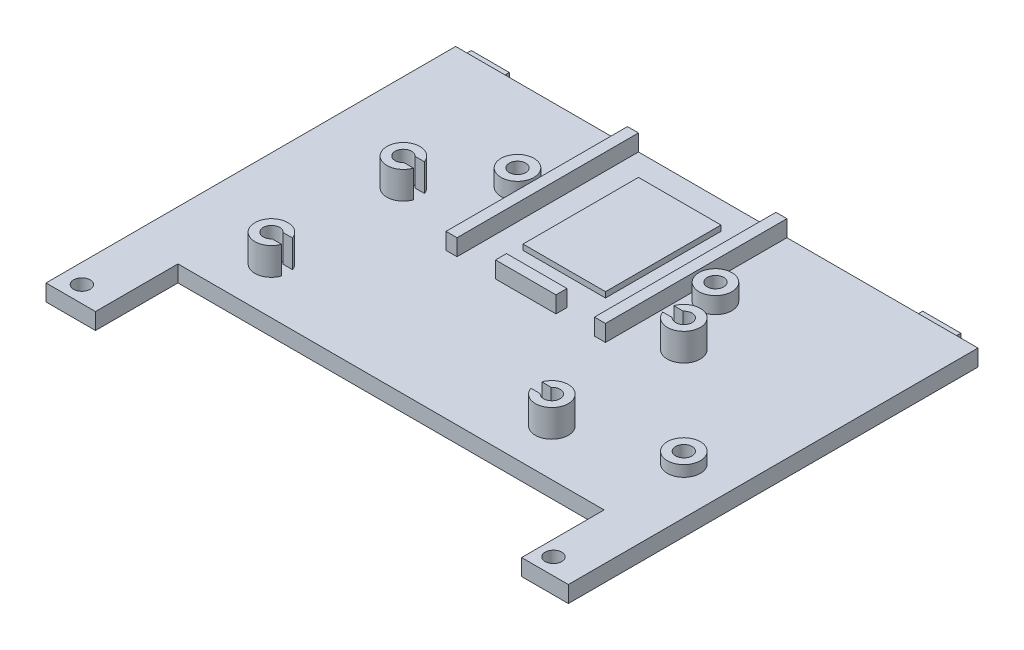
SolidWorks part; units mm, degrees
ref_plane "Front Plane" through (0, 0, 0) normal (0, 0, 1) x (1, 0, 0)
ref_plane "Top Plane" through (0, 0, 0) normal (0, 1, 0) x (1, 0, 0)
ref_plane "Right Plane" through (0, 0, 0) normal (1, 0, 0) x (0, 0, -1)
sketch "Sketch1" plane through (0, 0, 0) normal (0, 1, 0) x (1, 0, 0)
  line L1 (-53.25, 37.25) -> (53.25, 37.25)
  line L2 (-53.25, 37.25) -> (-53.25, -37.25)
  line L3 (-53.25, -37.25) -> (53.25, -37.25)
  line L4 (53.25, 37.25) -> (53.25, -37.25)
  dimension "D1" = 106.5
  dimension "D2" = 74.5
  dimension "D3" = 37.25
  dimension "D4" = 53.25
extrude "Boss-Extrude1" add sketch "Sketch1" along normal blind 3
sketch "Sketch2" plane through (0, 3, 0) normal (0, 1, 0) x (1, 0, 0)
  line L0 (53.25, 37.25) -> (-53.25, 37.25) construction
  line L1 (-47.265, 37.25) -> (-40.335, 37.25)
  line L2 (-47.265, 37.25) -> (-47.265, 39.1)
  line L3 (-47.265, 39.1) -> (-40.335, 39.1)
  line L4 (-40.335, 37.25) -> (-40.335, 39.1)
  line L5 (-53.25, 37.25) -> (-53.25, -37.25) construction
  line L6 (34.85, 37.25) -> (41.78, 37.25)
  line L7 (34.85, 37.25) -> (34.85, 39.1)
  line L8 (34.85, 39.1) -> (41.78, 39.1)
  line L9 (41.78, 37.25) -> (41.78, 39.1)
  line L10 (53.25, -37.25) -> (53.25, 37.25) construction
  dimension "D1" = 5.985
  dimension "D2" = 6.93
  dimension "D3" = 11.47
  dimension "D4" = 1.85
  dimension "D5" = 6.93
  dimension "D6" = 1.85
extrude "Boss-Extrude2" add sketch "Sketch2" against normal blind 3
sketch "Sketch3" plane through (0, 3, 0) normal (0, 1, 0) x (1, 0, 0)
  line L1 (-47.265, 39.1) -> (-40.335, 39.1)
  line L2 (-47.265, 39.1) -> (-47.265, 37.25)
  line L3 (-47.265, 37.25) -> (-40.335, 37.25)
  line L4 (-40.335, 39.1) -> (-40.335, 37.25)
  line L5 (34.85, 39.1) -> (41.78, 39.1)
  line L6 (34.85, 39.1) -> (34.85, 37.25)
  line L7 (34.85, 37.25) -> (41.78, 37.25)
  line L8 (41.78, 39.1) -> (41.78, 37.25)
extrude "Cut-Extrude1" cut sketch "Sketch3" against normal blind 1.07
sketch "Sketch4" plane through (0, 3, 0) normal (0, 1, 0) x (1, 0, 0)
  line L0 (-53.25, 37.25) -> (-53.25, -37.25) construction
  line L1 (-53.25, 32.25) -> (-48.25, 32.25)
  line L2 (-53.25, 32.25) -> (-53.25, -32.25)
  line L3 (-53.25, -32.25) -> (-48.25, -32.25)
  line L4 (-48.25, 32.25) -> (-48.25, -32.25)
  line L5 (53.25, 37.25) -> (-53.25, 37.25) construction
  line L6 (-53.25, -37.25) -> (53.25, -37.25) construction
  line L7 (53.25, -37.25) -> (53.25, 37.25) construction
  line L8 (-39.25, -37.25) -> (39.25, -37.25)
  line L9 (-39.25, -37.25) -> (-39.25, -22.25)
  line L10 (-39.25, -22.25) -> (39.25, -22.25)
  line L11 (39.25, -37.25) -> (39.25, -22.25)
  dimension "D1" = 5
  dimension "D2" = 5
  dimension "D3" = 5
  dimension "D4" = 14
  dimension "D5" = 14
  dimension "D6" = 15
extrude "Cut-Extrude2" cut sketch "Sketch4" against normal blind 3
sketch "Sketch5" plane through (0, 3, 0) normal (0, 1, 0) x (1, 0, 0)
  circle A0 centre (-53.25, -37.25) radius 3.5
  circle A1 centre (53.25, -37.25) radius 3.5
  circle A2 centre (53.25, 37.25) radius 3.5
  circle A3 centre (-53.25, 37.25) radius 3.5
  dimension "D1" = 7
  dimension "D2" = 7
  dimension "D3" = 7
  dimension "D4" = 7
extrude "Cut-Extrude3" cut sketch "Sketch5" against normal blind 3
sketch "Sketch6" plane through (0, 3, 0) normal (0, 1, 0) x (1, 0, 0)
  line L0 (39.25, -22.25) -> (-39.25, -22.25) construction
  line L1 (-33.25, 12.75) -> (22.75, 12.75)
  line L2 (-33.25, 12.75) -> (-33.25, -16.25)
  line L3 (-33.25, -16.25) -> (22.75, -16.25)
  line L4 (22.75, 12.75) -> (22.75, -16.25)
  line L5 (-48.25, -32.25) -> (-48.25, 32.25) construction
  line L7 (-30.75, -14.75) -> (-27.3508, -14.75)
  line L8 (-30.75, -14.75) -> (-30.75, -12.75)
  line L9 (-30.75, -12.75) -> (-27.3508, -12.75)
  line L10 (-27.3508, -14.75) -> (-27.3508, -12.75)
  line L11 (-30.75, 11.25) -> (-27.35, 11.25)
  line L12 (-30.75, 11.25) -> (-30.75, 9.25)
  line L13 (-30.75, 9.25) -> (-27.35, 9.25)
  line L14 (-27.35, 11.25) -> (-27.35, 9.25)
  line L15 (20.25, 9.25) -> (16.85, 9.25)
  line L16 (20.25, 9.25) -> (20.25, 11.25)
  line L17 (20.25, 11.25) -> (16.85, 11.25)
  line L18 (16.85, 9.25) -> (16.85, 11.25)
  line L19 (20.25, -12.75) -> (16.85, -12.75)
  line L20 (20.25, -12.75) -> (20.25, -14.75)
  line L21 (20.25, -14.75) -> (16.85, -14.75)
  line L22 (16.85, -12.75) -> (16.85, -14.75)
  circle A0 centre (-30.75, -13.75) radius 1.5
  circle A1 centre (20.25, -13.75) radius 1.5
  circle A2 centre (20.25, 10.25) radius 1.5
  circle A3 centre (-30.75, 10.25) radius 1.5
  circle A4 centre (-30.75, -13.75) radius 3
  circle A5 centre (20.25, -13.75) radius 3
  circle A6 centre (20.25, 10.25) radius 3
  circle A7 centre (-30.75, 10.25) radius 3
  dimension "D6" = 3
  dimension "D14" = 3
  dimension "D15" = 3
  dimension "D16" = 3
  dimension "D17" = 6
  dimension "D18" = 6
  dimension "D19" = 6
  dimension "D20" = 6
  dimension "D21" = 1
  dimension "D1" = 29
  dimension "D2" = 56
  dimension "D3" = 6
  dimension "D4" = 15
  dimension "D5" = 2.5
  dimension "D7" = 2.5
  dimension "D8" = 2.5
  dimension "D9" = 2.5
  dimension "D10" = 2.5
  dimension "D11" = 2.5
  dimension "D12" = 2.5
  dimension "D13" = 2.5
  dimension "D22" = 2
  dimension "D23" = 3.3992
  dimension "D24" = 0
  dimension "D25" = 0
  dimension "D26" = 1
  dimension "D27" = 2
  dimension "D28" = 3.4
  dimension "D29" = 0
  dimension "D30" = 1
  dimension "D31" = 2
  dimension "D32" = 3.4
  dimension "D33" = 0
  dimension "D34" = 1
  dimension "D35" = 2
  dimension "D36" = 3.4
extrude "Boss-Extrude5" add sketch "Sketch6" along normal blind 5 contours L11 A7 L1 L2 L13 A3 | L2 A7 | L1 A7 | L3 A4 L7 A0 L9 L2 | L2 A4 | L3 A4 | L3 A5 L4 L19 A1 L21 | L3 A5 | L4 A5 | L4 A6 L1 L17 A2 L15 | L4 A6 | L1 A6
sketch "Sketch9" plane through (0, 3, 0) normal (0, 1, 0) x (1, 0, 0)
  line L0 (49.75, 37.25) -> (-49.75, 37.25) construction
  line L1 (53.25, -33.75) -> (53.25, 33.75) construction
  circle A0 centre (38.25, -7.75) radius 3
  circle A1 centre (38.25, -7.75) radius 1.5
  dimension "D3" = 6
  dimension "D4" = 3
  dimension "D1" = 45
  dimension "D2" = 15
extrude "Boss-Extrude6" add sketch "Sketch9" along normal blind 2
sketch "Sketch10" plane through (0, 3, 0) normal (0, 1, 0) x (1, 0, 0)
  line L0 (49.75, 37.25) -> (-49.75, 37.25) construction
  line L1 (-15, 37.25) -> (10, 37.25)
  line L2 (-15, 37.25) -> (-15, 6.25)
  line L3 (-15, 6.25) -> (10, 6.25)
  line L4 (10, 37.25) -> (10, 6.25)
  line L5 (53.25, -33.75) -> (53.25, 33.75) construction
  line L7 (-10, 32.25) -> (5, 32.25)
  line L8 (-10, 32.25) -> (-10, 11.25)
  line L9 (-10, 11.25) -> (5, 11.25)
  line L10 (5, 32.25) -> (5, 11.25)
  line L11 (-17, 37.25) -> (12, 37.25)
  line L12 (-17, 37.25) -> (-17, 4.25)
  line L13 (-17, 4.25) -> (12, 4.25)
  line L14 (12, 37.25) -> (12, 4.25)
  line M41 (49.75, 37.25) -> (-49.75, 37.25)
  dimension "D1" = 43.25
  dimension "D2" = 25
  dimension "D3" = 38.25
  dimension "D4" = 31
  dimension "D5" = 5
  dimension "D6" = 5
  dimension "D7" = 5
  dimension "D8" = 5
  dimension "D9" = 2
  dimension "D10" = 2
  dimension "D11" = 2
extrude "Boss-Extrude7" add sketch "Sketch10" along normal blind 1 contours L10 L7 L8 L9 | L14 L4 L3 L2 L12 L13 M41
sketch "Sketch11" plane through (0, 4, 0) normal (0, 1, 0) x (1, 0, 0)
  line L0 (-17, 4.25) -> (12, 4.25) construction
  line L1 (-17, 37.25) -> (-15, 37.25)
  line L2 (-17, 37.25) -> (-17, 4.25)
  line L3 (-17, 4.25) -> (-15, 4.25)
  line L4 (-15, 37.25) -> (-15, 4.25)
  line L6 (12, 37.25) -> (10, 37.25)
  line L7 (12, 37.25) -> (12, 4.25)
  line L8 (12, 4.25) -> (10, 4.25)
  line L9 (10, 37.25) -> (10, 4.25)
  line L10 (-17, 4.25) -> (12, 4.25)
  line L11 (-17, 4.25) -> (-17, 6.25)
  line L12 (-17, 6.25) -> (12, 6.25)
  line L13 (12, 4.25) -> (12, 6.25)
  line M7 (12, 4.25) -> (12, 37.25)
  line M8 (12, 37.25) -> (10, 37.25)
  line M9 (10, 37.25) -> (10, 6.25)
  line M10 (10, 6.25) -> (-15, 6.25)
  line M14 (-17, 4.25) -> (12, 4.25)
  dimension "D1" = 2
  dimension "D2" = 2
  dimension "D3" = 2
extrude "Boss-Extrude8" add sketch "Sketch11" along normal blind 2 contours L9 L4 M10 M14 | L12 L9 M14 M7 | L12 L7 M9 M8
sketch "Sketch12" plane through (0, 3, 0) normal (0, 1, 0) x (1, 0, 0)
  line L1 (-53.25, 32.25) -> (-48.25, 32.25)
  line L2 (-53.25, 32.25) -> (-53.25, 37.25)
  line L3 (-53.25, 37.25) -> (-48.25, 37.25)
  line L4 (-48.25, 32.25) -> (-48.25, 37.25)
  line L6 (-48.25, -32.25) -> (-53.25, -32.25)
  line L7 (-48.25, -32.25) -> (-48.25, -37.25)
  line L8 (-48.25, -37.25) -> (-53.25, -37.25)
  line L9 (-53.25, -32.25) -> (-53.25, -37.25)
  dimension "D1" = 5
  dimension "D2" = 5
extrude "Cut-Extrude4" cut sketch "Sketch12" against normal blind 4
sketch "Sketch13" plane through (0, 6, 0) normal (0, 1, 0) x (1, 0, 0)
  line L0 (12, 4.25) -> (12, 37.25) construction
  line L1 (12, 27.75) -> (-17, 27.75)
  line L2 (12, 27.75) -> (12, 13.75)
  line L3 (12, 13.75) -> (-17, 13.75)
  line L4 (-17, 27.75) -> (-17, 13.75)
  line L5 (-17, 37.25) -> (-17, 4.25) construction
  dimension "D1" = 7.5
  dimension "D2" = 14
sketch "Sketch14" plane through (0, 3, 0) normal (0, 1, 0) x (1, 0, 0)
  line L1 (49.75, -37.25) -> (53.75, -37.25)
  line L2 (49.75, -37.25) -> (49.75, 38.0641)
  line L3 (49.75, 38.0641) -> (53.75, 38.0641)
  line L4 (53.75, -37.25) -> (53.75, 38.0641)
  dimension "D1" = 4
extrude "Cut-Extrude5" cut sketch "Sketch14" against normal blind 10
sketch "Sketch15" plane through (0, 3, 0) normal (0, 1, 0) x (1, 0, 0)
  line L2 (12, 13.75) -> (-17, 13.75) construction
  line L3 (12, 27.75) -> (-17, 27.75) construction
  line L4 (12, 27.75) -> (12, 13.75) construction
  line L5 (-17, 27.75) -> (-17, 13.75) construction
  circle A0 centre (15.5, 20.75) radius 3
  circle A1 centre (-20.5, 20.75) radius 3
  circle A2 centre (15.5, 20.75) radius 1.5
  circle A3 centre (-20.5, 20.75) radius 1.5
  dimension "D1" = 6
  dimension "D2" = 6
  dimension "D8" = 3
  dimension "D9" = 3
  dimension "D3" = 7
  dimension "D4" = 7
  dimension "D5" = 3.5
  dimension "D6" = 7
  dimension "D7" = 3.5
  dimension "D10" = 36
extrude "Boss-Extrude9" add sketch "Sketch15" along normal blind 3
sketch "Sketch16" plane through (0, 3, 0) normal (0, 1, 0) x (1, 0, 0)
  circle A0 centre (15.5, 20.75) radius 1.5
  circle A1 centre (-20.5, 20.75) radius 1.5
  dimension "D1" = 3
  dimension "D2" = 3
extrude "Cut-Extrude6" cut sketch "Sketch16" against normal blind 3
sketch "Sketch17" plane through (0, 3, 0) normal (0, 1, 0) x (1, 0, 0)
  circle A0 centre (38.25, -7.75) radius 1.5
  dimension "D1" = 3
extrude "Cut-Extrude7" cut sketch "Sketch17" against normal blind 3
sketch "Sketch18" plane through (0, 6, 0) normal (0, 1, 0) x (1, 0, 0)
  line L0 (-17, 4.25) -> (12, 4.25) construction
  line L1 (10, 6.25) -> (3, 6.25)
  line L2 (10, 6.25) -> (10, 4.25)
  line L3 (10, 4.25) -> (3, 4.25)
  line L4 (3, 6.25) -> (3, 4.25)
  line L6 (-15, 6.25) -> (-8, 6.25)
  line L7 (-15, 6.25) -> (-15, 4.25)
  line L8 (-15, 4.25) -> (-8, 4.25)
  line L9 (-8, 6.25) -> (-8, 4.25)
  dimension "D1" = 7
  dimension "D2" = 7
extrude "Cut-Extrude8" cut sketch "Sketch18" against normal blind 3
sketch "Sketch19" plane through (0, 3, 0) normal (0, 1, 0) x (1, 0, 0)
  line L0 (41.78, 37.25) -> (41.78, 39.1) construction
  line L3 (-47.265, 39.1) -> (-47.265, 37.25) construction
  line L4 (39.25, -37.25) -> (49.75, -37.25) construction
  line L5 (-48.25, -37.25) -> (-39.25, -37.25) construction
  circle A0 centre (41.035, -34.25) radius 1.5
  circle A1 centre (-44.73, -34.25) radius 1.5
  dimension "D1" = 3
  dimension "D2" = 3
  dimension "D3" = 0.745
  dimension "D4" = 2.535
  dimension "D5" = 3
  dimension "D6" = 3
extrude "Cut-Extrude9" cut sketch "Sketch19" against normal blind 3
sketch "Sketch20" plane through (0, 3, 0) normal (0, 1, 0) x (1, 0, 0)
  line L0 (49.75, 37.25) -> (12, 37.25) construction
  line L1 (49.75, -37.25) -> (46.75, -37.25)
  line L2 (49.75, -37.25) -> (49.75, 37.25)
  line L3 (49.75, 37.25) -> (46.75, 37.25)
  line L4 (46.75, -37.25) -> (46.75, 37.25)
  dimension "D1" = 3
extrude "Cut-Extrude10" cut sketch "Sketch20" against normal blind 8
sketch "Sketch21" plane through (0, 3, 0) normal (0, 1, 0) x (1, 0, 0)
  line L0 (39.25, -22.25) -> (-39.25, -22.25) construction
  line L1 (39.25, -37.25) -> (38.25, -37.25)
  line L2 (39.25, -37.25) -> (39.25, -22.25)
  line L3 (39.25, -22.25) -> (38.25, -22.25)
  line L4 (38.25, -37.25) -> (38.25, -22.25)
  dimension "1" = 1
extrude "Boss-Extrude10" add sketch "Sketch21" against normal blind 3
